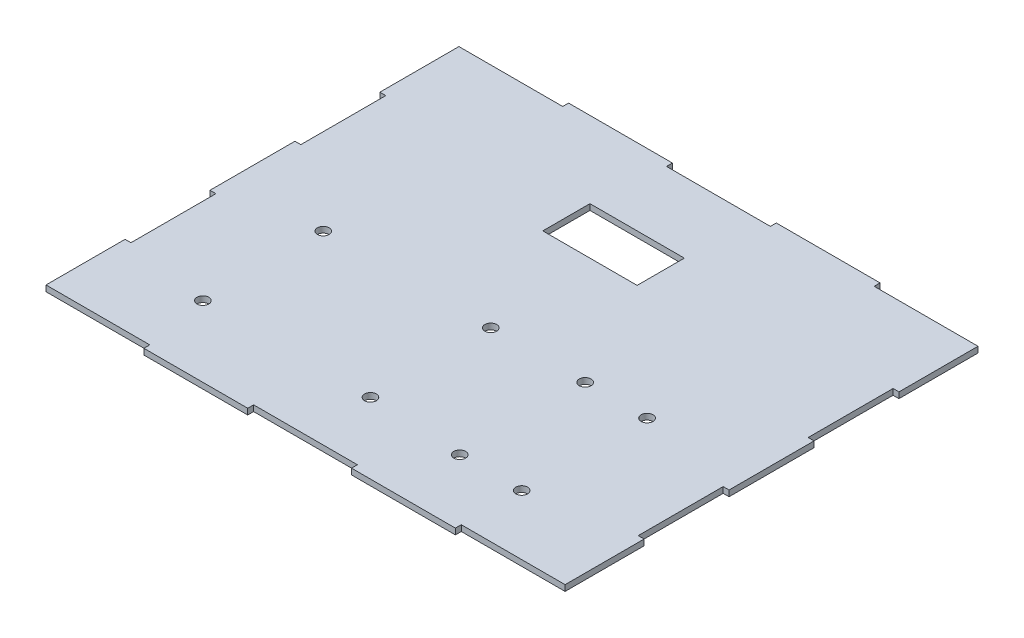
SolidWorks part; units mm, degrees
ref_plane "Front Plane" through (0, 0, 0) normal (0, 0, 1) x (1, 0, 0)
ref_plane "Top Plane" through (0, 0, 0) normal (0, 1, 0) x (1, 0, 0)
ref_plane "Right Plane" through (0, 0, 0) normal (1, 0, 0) x (0, 0, -1)
sketch "Sketch1" plane through (0, 0, 0) normal (0, 1, 0) x (1, 0, 0)
  line L1 (139.7, -114.3) -> (-139.7, -114.3)
  line L2 (139.7, -114.3) -> (139.7, 114.3)
  line L3 (139.7, 114.3) -> (-139.7, 114.3)
  line L4 (-139.7, -114.3) -> (-139.7, 114.3)
  line L5 (139.7, -114.3) -> (-139.7, 114.3) construction
  line L6 (139.7, 114.3) -> (-139.7, -114.3) construction
  point P0 (0, 0)
extrude "Boss-Extrude1" add sketch "Sketch1" along normal blind 3.175
sketch "Sketch3" plane through (0, 3.175, 0) normal (0, 1, 0) x (1, 0, 0)
  line L1 (-139.7, -111.125) -> (-139.7, -114.3)
  line L2 (-114.3, -114.3) -> (114.3, -114.3) construction
  line L3 (-139.7, -111.125) -> (-83.82, -111.125)
  line L4 (-139.7, -114.3) -> (-83.82, -114.3)
  line L5 (136.525, 68.58) -> (136.525, 22.86)
  line L6 (-83.82, -111.125) -> (-83.82, -114.3)
  line L7 (83.82, -111.125) -> (83.82, -114.3)
  line L8 (83.82, -114.3) -> (139.7, -114.3)
  line L9 (139.7, -111.125) -> (139.7, -114.3)
  line L10 (139.7, -114.3) -> (139.7, 114.3) construction
  line L11 (136.525, 68.58) -> (139.7, 68.58)
  line L12 (139.7, 68.58) -> (139.7, 22.86)
  line L13 (136.525, 22.86) -> (139.7, 22.86)
  line L14 (-136.525, -68.58) -> (-139.7, -68.58)
  line L15 (-139.7, -22.86) -> (-139.7, -68.58)
  line L16 (136.525, -22.86) -> (136.525, -68.58)
  line L17 (-136.525, -22.86) -> (-139.7, -22.86)
  line L18 (-136.525, -22.86) -> (-136.525, -68.58)
  line L19 (-136.525, 22.86) -> (-139.7, 22.86)
  line L20 (-139.7, 68.58) -> (-139.7, 22.86)
  line L21 (-136.525, 68.58) -> (-139.7, 68.58)
  line L22 (-136.525, 68.58) -> (-136.525, 22.86)
  line L23 (136.525, -22.86) -> (139.7, -22.86)
  line L24 (139.7, -22.86) -> (139.7, -68.58)
  line L25 (-27.94, 111.125) -> (27.94, 111.125)
  line L26 (83.82, -111.125) -> (139.7, -111.125)
  line L27 (-27.94, -111.125) -> (-27.94, -114.3)
  line L28 (-27.94, -114.3) -> (27.94, -114.3)
  line L29 (27.94, -111.125) -> (27.94, -114.3)
  line L30 (27.94, 111.125) -> (27.94, 114.3)
  line L31 (-27.94, 114.3) -> (27.94, 114.3)
  line L32 (-27.94, 111.125) -> (-27.94, 114.3)
  line L33 (83.82, 111.125) -> (139.7, 111.125)
  line L34 (139.7, 111.125) -> (139.7, 114.3)
  line L35 (83.82, 114.3) -> (139.7, 114.3)
  line L36 (83.82, 111.125) -> (83.82, 114.3)
  line L37 (-83.82, 111.125) -> (-83.82, 114.3)
  line L38 (-139.7, 114.3) -> (-83.82, 114.3)
  line L39 (-139.7, 111.125) -> (-83.82, 111.125)
  line L40 (-139.7, 111.125) -> (-139.7, 114.3)
  line L41 (136.525, -68.58) -> (139.7, -68.58)
  line L42 (19.5919, 47.7672) -> (-31.2081, 47.7672)
  line L43 (19.5919, 47.7672) -> (19.5919, 73.1672)
  line L44 (19.5919, 73.1672) -> (-31.2081, 73.1672)
  line L45 (-31.2081, 47.7672) -> (-31.2081, 73.1672)
  line L46 (19.5919, 47.7672) -> (-31.2081, 73.1672) construction
  line L47 (19.5919, 73.1672) -> (-31.2081, 47.7672) construction
  line L49 (-139.7, 114.3) -> (-139.7, -114.3) construction
  line L50 (139.7, 114.3) -> (-139.7, 114.3) construction
  line L51 (-27.94, -111.125) -> (27.94, -111.125)
  circle A0 centre (0, -11.43) radius 3.175
  circle A1 centre (-90.17, -11.43) radius 3.175
  circle A2 centre (-90.17, -76.2) radius 3.175
  circle A3 centre (0, -76.2) radius 3.175
  circle A4 centre (84.1303, -78.93) radius 3.175
  circle A5 centre (84.1303, -11.43) radius 3.175
  circle A6 centre (50.8, -11.43) radius 3.175
  circle A7 centre (50.8, -78.93) radius 3.175
  point P0 (-5.8081, 60.4672)
  dimension "D9" = 6.35
  dimension "D10" = 6.35
  dimension "D11" = 6.35
  dimension "D12" = 6.35
  dimension "D20" = 6.35
  dimension "D21" = 6.35
  dimension "D24" = 6.35
  dimension "D25" = 6.35
  dimension "D33" = 0
  dimension "D4" = 90.17
  dimension "D5" = 3.175
  dimension "D6" = 3.175
  dimension "D7" = 90.17
  dimension "D8" = 64.77
  dimension "D13" = 38.1
  dimension "D14" = 0
  dimension "D15" = 0
  dimension "D18" = 139.7
  dimension "D19" = 139.7
  dimension "D23" = 67.5
  dimension "D26" = 67.5
  dimension "D27" = 0
  dimension "D28" = 0
  dimension "D29" = 50.8
  dimension "D30" = 33.3303
  dimension "D31" = 33.3303
  dimension "D32" = 50.8
  dimension "D34" = 3.175
  dimension "D35" = 0
extrude "Cut-Extrude1" cut sketch "Sketch3" against normal blind 6.35
